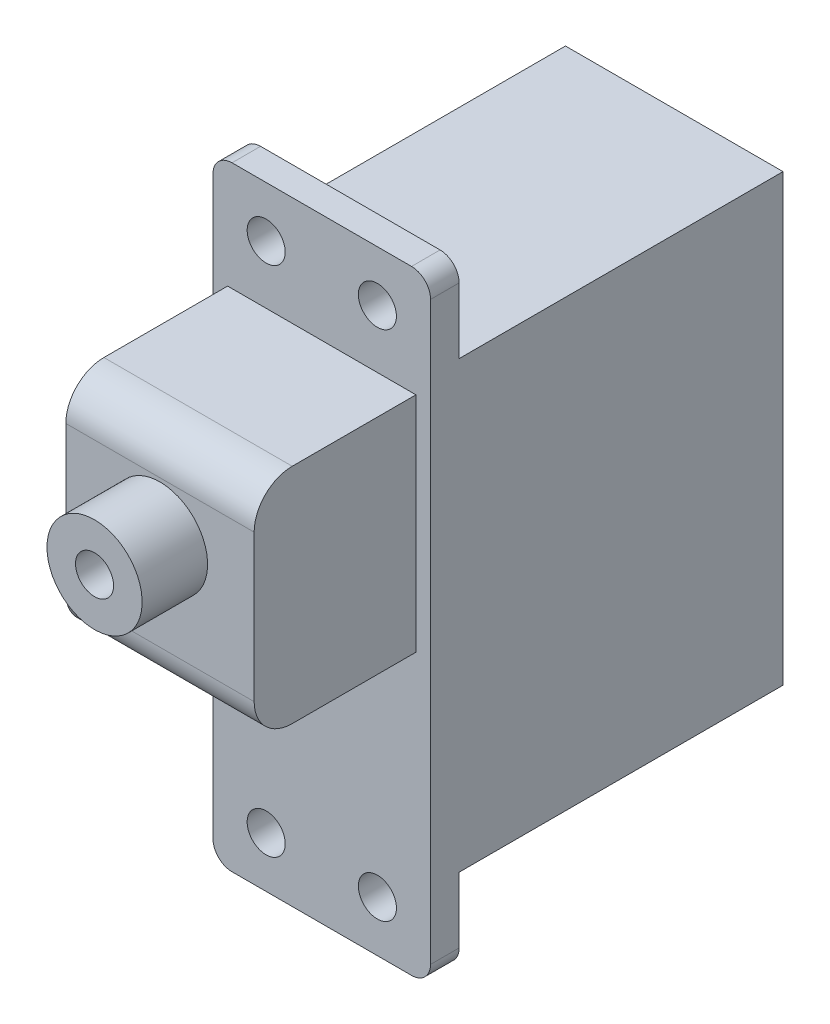
SolidWorks part; units mm, degrees
material "Cuivre"
ref_plane "Plan de face" through (0, 0, 0) normal (0, 0, 1) x (1, 0, 0)
ref_plane "Plan de dessus" through (0, 0, 0) normal (0, 1, 0) x (1, 0, 0)
ref_plane "Plan de droite" through (0, 0, 0) normal (1, 0, 0) x (0, 0, -1)
ref_plane "Plan1" through (11.43, 0, 0) normal (1, 0, 0) x (0, 0, -1)
sketch "Esquisse1" plane through (11.43, 0, 0) normal (1, 0, 0) x (0, 0, -1)
  line L0 (-1.5, -4.445) -> (17.018, -4.445)
  line L1 (17.018, -4.445) -> (17.018, 27.813)
  line L2 (17.018, 27.813) -> (-1.5, 27.813)
  line L3 (-1.5, 27.813) -> (-1.5, -4.445)
extrude "Boss.-Extru.1" add sketch "Esquisse1" against normal blind 11.43
sketch "Esquisse2" plane through (0, 0, 0) normal (-1, 0, 0) x (0, 0, 1)
  line L0 (0, 0) -> (-17.018, 0)
  line L1 (-17.018, 0) -> (-17.018, -4.445)
  line L2 (-17.018, -4.445) -> (0, -4.445)
  line L3 (0, -4.445) -> (0, 0)
extrude "Enlèv. mat.-Extru.1" cut sketch "Esquisse2" against normal through all
sketch "Esquisse3" plane through (0, 0, 0) normal (-1, 0, 0) x (0, 0, 1)
  line L0 (-17.018, 23.368) -> (0, 23.368)
  line L1 (0, 23.368) -> (0, 27.813)
  line L2 (0, 27.813) -> (-17.018, 27.813)
  line L3 (-17.018, 27.813) -> (-17.018, 23.368)
extrude "Enlèv. mat.-Extru.2" cut sketch "Esquisse3" against normal through all
sketch "Esquisse4" plane through (0, 0, 1.5) normal (0, 0, 1) x (1, 0, 0)
  line L0 (0.7681, 22.0878) -> (10.6619, 22.0878)
  line L1 (10.6619, 22.0878) -> (10.6619, 10.3767)
  line L2 (10.6619, 10.3767) -> (0.7681, 10.3767)
  line L3 (0.7681, 10.3767) -> (0.7681, 22.0878)
extrude "Boss.-Extru.2" add sketch "Esquisse4" along normal blind 8.5
ref_plane "Plan2" through (0, 17.399, 0) normal (0, -1, 0) x (1, 0, 0)
sketch "Esquisse5" plane through (0, 17.399, 0) normal (0, -1, 0) x (1, 0, 0)
  line L0 (8.215, 13.438) -> (5.715, 13.438)
  line L1 (5.715, 13.438) -> (5.715, 10)
  line L2 (5.715, 10) -> (8.215, 10)
  line L3 (8.215, 10) -> (8.215, 13.438)
  line L4 (5.715, 13.438) -> (5.715, 10) construction
revolve "Révolution1" add sketch "Esquisse5" angle 360 about L4
hole_wizard "Diamètre du perçage Ø2.0 (2)1" positions "Esquisse7" profile "Esquisse6" hole size "Ø2.0" standard "Ansi Metric"
sketch "Esquisse7" plane through (0, 0, 13.438) normal (0, 0, 1) x (1, 0, 0)
  point P0 (5.715, 17.399)
sketch "Esquisse6" plane through (5.715, 17.399, 13.438) normal (1, 0, 0) x (0, -1, 0)
  line L0 (0, 0) -> (0, 2)
  line L1 (0, 2) -> (1, 2)
  line L2 (1, 2) -> (1, 0)
  line L5 (1, 0) -> (0, 0)
  line L10 (0, 2) -> (-1, 2) construction
  line L11 (0, -6.35) -> (0, 107.95) construction
  dimension "Diamètre du perçage" = 2
  dimension "Profondeur du perçage" = 2
  dimension "Angle de pointe" = 180
hole_wizard "Diamètre du perçage Ø2.0 (2)2" positions "Esquisse9" profile "Esquisse8" hole size "Ø2.0" standard "Ansi Metric"
sketch "Esquisse9" plane through (0, 0, 0) normal (0, 0, -1) x (-1, 0, 0)
  point P0 (-2.794, -1.778)
  point P1 (-8.636, -1.778)
  point P2 (-8.636, 25.146)
  point P3 (-2.794, 25.146)
sketch "Esquisse8" plane through (2.794, -1.778, 0) normal (1, 0, 0) x (0, 1, 0)
  line L0 (0, 0) -> (0, 13.438)
  line L1 (0, 13.438) -> (1, 13.438)
  line L2 (1, 13.438) -> (1, 0)
  line L5 (1, 0) -> (0, 0)
  line L11 (0, -6.35) -> (0, 107.95) construction
  dimension "Diamètre du perçage jusqu'au prochain" = 2
  dimension "Profondeur du perçage jusqu'au prochain" = 13.438
fillet "Congé1" radius 1 4 edges at (11.43, -4.445, 0.75) (0, 27.813, 0.75) (11.43, 27.813, 0.75) (0, -4.445, 0.75)
fillet "Congé2" radius 2 2 edges at (5.715, 10.3767, 10) (5.715, 22.0878, 10)
